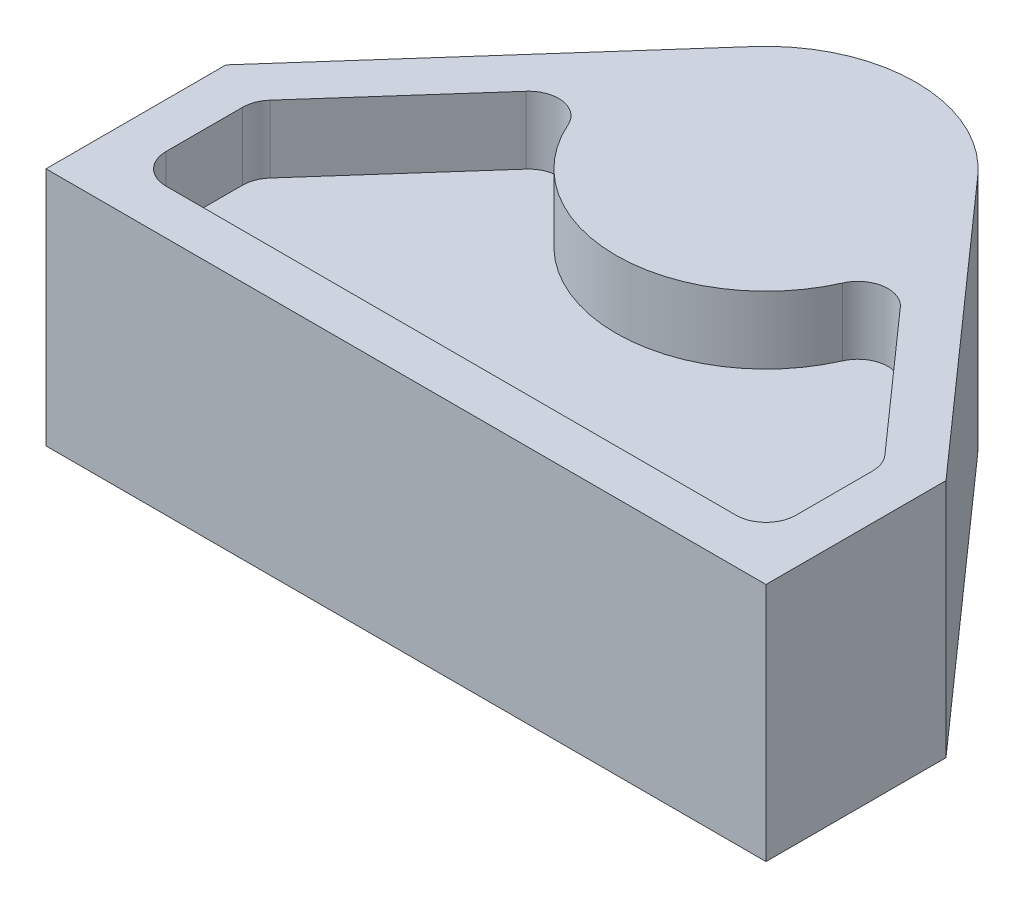
SolidWorks part; units mm, degrees
ref_plane "Front Plane" through (0, 0, 0) normal (0, 0, 1) x (1, 0, 0)
ref_plane "Top Plane" through (0, 0, 0) normal (0, 1, 0) x (1, 0, 0)
ref_plane "Right Plane" through (0, 0, 0) normal (1, 0, 0) x (0, 0, -1)
sketch "Sketch1" plane through (0, 0, 0) normal (0, 1, 0) x (1, 0, 0)
  line L1 (-38.1, 9.525) -> (38.1, 9.525)
  line L2 (-38.1, 9.525) -> (-38.1, -9.525)
  line L3 (-38.1, -9.525) -> (38.1, -9.525)
  line L4 (38.1, 9.525) -> (38.1, -9.525)
  line L5 (-38.1, 9.525) -> (38.1, -9.525) construction
  line L6 (-38.1, -9.525) -> (38.1, 9.525) construction
  point P0 (0, 0)
  dimension "D1" = 19.05
  dimension "D2" = 76.2
extrude "Boss-Extrude1" add sketch "Sketch1" along normal blind 25.4
sketch "Sketch2" plane through (0, 0, 0) normal (0, 1, 0) x (1, 0, 0)
  line L0 (0, 28.575) -> (0, 0) construction
  line L1 (-38.1, -9.525) -> (38.1, -9.525) construction
  line L2 (-38.1, 9.525) -> (-11.8797, 39.1053)
  line L3 (38.1, 9.525) -> (11.8797, 39.1053)
  line L8 (38.1, -9.525) -> (38.1, 9.525)
  line L9 (38.1, 9.525) -> (-38.1, 9.525)
  line L10 (-38.1, 9.525) -> (-38.1, -9.525)
  line L11 (-38.1, -9.525) -> (38.1, -9.525)
  line L12 (38.1, -9.525) -> (38.1, 9.525)
  line L14 (-38.1, 9.525) -> (-38.1, -9.525)
  line L15 (-38.1, -9.525) -> (38.1, -9.525)
  arc A0 (11.8797, 39.1053) -> (-11.8797, 39.1053) centre (0, 28.575) ccw
  dimension "D1" = 31.75
  dimension "D2" = 38.1
  dimension "D3" = 0
extrude "Boss-Extrude2" add sketch "Sketch2" along normal blind 25.4
sketch "Sketch3" plane through (0, 25.4, 0) normal (0, 1, 0) x (1, 0, 0)
  line L9 (-33.3375, -4.7625) -> (38.1, -4.7625)
  line L10 (-33.3375, 7.7181) -> (-33.3375, -4.7625)
  line L11 (-8.3158, 35.9462) -> (-33.3375, 7.7181)
  line L12 (-30.1625, -4.7625) -> (30.1625, -4.7625)
  line L13 (-33.3375, 6.5135) -> (-33.3375, -1.5875)
  line L14 (-19.803, 22.987) -> (-32.5384, 8.6195)
  line L17 (33.3375, -9.525) -> (33.3375, 7.7181)
  line L18 (33.3375, 7.7181) -> (8.3158, 35.9462)
  line L19 (33.3375, -1.5875) -> (33.3375, 6.5135)
  line L20 (32.5384, 8.6195) -> (19.803, 22.987)
  arc A0 (-14.5226, 22.1632) -> (14.5226, 22.1632) centre (0, 28.575) ccw
  arc A1 (11.8797, 39.1053) -> (-11.8797, 39.1053) centre (0, 28.575) ccw construction
  arc A2 (-33.3375, 6.5135) -> (-32.5384, 8.6195) centre (-30.1625, 6.5135) cw
  arc A3 (-30.1625, -4.7625) -> (-33.3375, -1.5875) centre (-30.1625, -1.5875) cw
  arc A4 (30.1625, -4.7625) -> (33.3375, -1.5875) centre (30.1625, -1.5875) ccw
  arc A5 (33.3375, 6.5135) -> (32.5384, 8.6195) centre (30.1625, 6.5135) ccw
  arc A6 (14.5226, 22.1632) -> (19.803, 22.987) centre (17.4271, 20.8809) cw
  arc A7 (-19.803, 22.987) -> (-14.5226, 22.1632) centre (-17.4271, 20.8809) cw
  dimension "D3" = 3.175
  dimension "D1" = 4.7625
  dimension "D2" = 4.7625
extrude "Cut-Extrude1" cut sketch "Sketch3" against normal blind 7.1374
